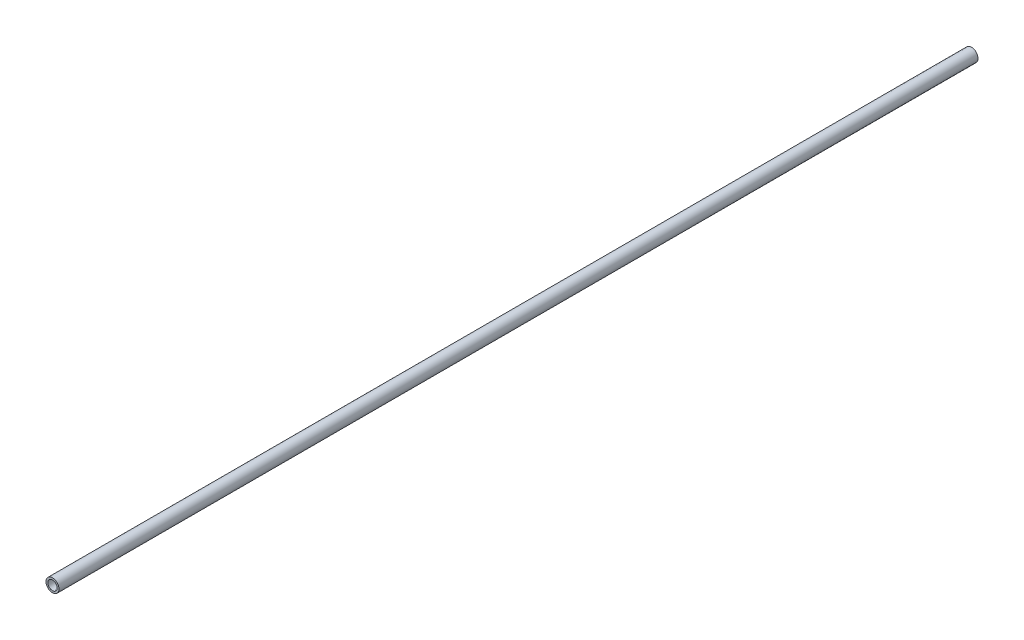
SolidWorks part; units mm, degrees
ref_plane "Front Plane" through (0, 0, 0) normal (0, 0, 1) x (1, 0, 0)
ref_plane "Top Plane" through (0, 0, 0) normal (0, 1, 0) x (1, 0, 0)
ref_plane "Right Plane" through (0, 0, 0) normal (1, 0, 0) x (0, 0, -1)
sketch "Sketch1" plane through (0, 0, 0) normal (0, 0, 1) x (1, 0, 0)
  circle A0 centre (203.5327, -1.7759) radius 3.5
  circle A1 centre (203.5327, -1.7759) radius 2.5
extrude "Boss-Extrude1" add sketch "Sketch1" against normal blind 495
